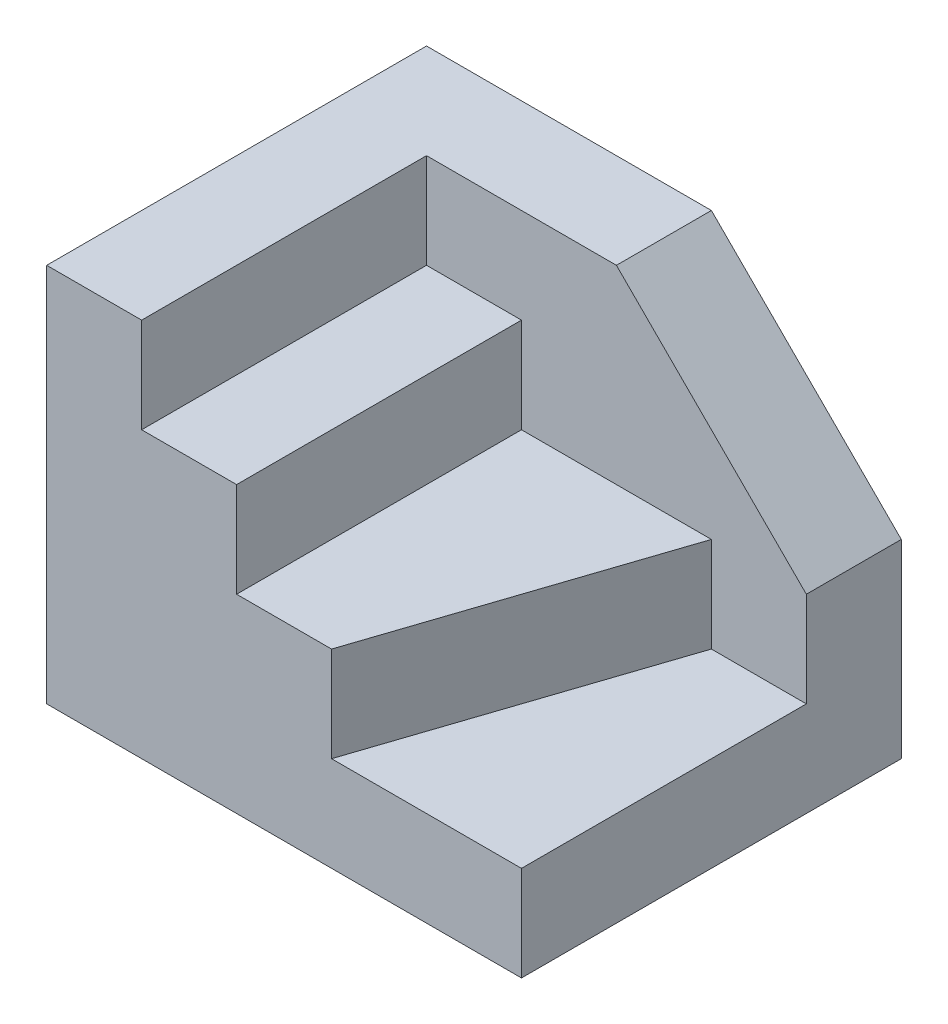
SolidWorks part; units mm, degrees
ref_plane "Front Plane" through (0, 0, 0) normal (0, 0, 1) x (1, 0, 0)
ref_plane "Top Plane" through (0, 0, 0) normal (0, 1, 0) x (1, 0, 0)
ref_plane "Right Plane" through (0, 0, 0) normal (1, 0, 0) x (0, 0, -1)
sketch "Sketch1" plane through (0, 0, 0) normal (0, 1, 0) x (1, 0, 0)
  line L1 (25, -20) -> (-25, -20)
  line L2 (25, -20) -> (25, 20)
  line L3 (25, 20) -> (-25, 20)
  line L4 (-25, -20) -> (-25, 20)
  line L5 (25, -20) -> (-25, 20) construction
  line L6 (25, 20) -> (-25, -20) construction
  point P0 (0, 0)
  dimension "D1" = 40
  dimension "D2" = 50
extrude "Boss-Extrude1" add sketch "Sketch1" along normal blind 40
sketch "Sketch3" plane through (0, 0, 20) normal (0, 0, 1) x (1, 0, 0)
  line L0 (-15, 40) -> (-15, 30)
  line L1 (-25, 40) -> (25, 40) construction
  line L2 (-15, 30) -> (-5, 30)
  line L3 (-5, 30) -> (-5, 20)
  line L4 (-5, 20) -> (25, 20)
  line L5 (25, 40) -> (25, 0) construction
  line L6 (-25, 40) -> (-25, 0) construction
  line L7 (-15, 40) -> (25, 40)
  line L8 (25, 40) -> (25, 20)
  dimension "D1" = 10
  dimension "D2" = 10
  dimension "D3" = 10
  dimension "D4" = 10
extrude "Cut-Extrude1" cut sketch "Sketch3" against normal offset from surface (30 mm away) 10 up to face at (0, 20, -20)
sketch "Sketch4" plane through (0, 20, 0) normal (0, 1, 0) x (1, 0, 0)
  line L0 (15, 10) -> (5, -20)
  line L1 (25, 10) -> (-5, 10) construction
  line L2 (-5, -20) -> (25, -20) construction
  line L3 (5, -20) -> (25, -20)
  line L4 (25, -20) -> (25, 10)
  line L5 (25, 10) -> (15, 10)
  dimension "D1" = 10
  dimension "D2" = 10
  dimension "D3" = 71.565
extrude "Cut-Extrude2" cut sketch "Sketch4" against normal blind 10
sketch "Sketch5" plane through (0, 0, -10) normal (0, 0, 1) x (1, 0, 0)
  line L0 (5, 40) -> (25, 20)
  line L1 (-15, 40) -> (25, 40) construction
  line L2 (25, 40) -> (25, 10) construction
  line L3 (25, 20) -> (25, 40)
  line L4 (25, 40) -> (5, 40)
  dimension "D1" = 45
  dimension "D2" = 30
extrude "Cut-Extrude3" cut sketch "Sketch5" against normal blind 10
